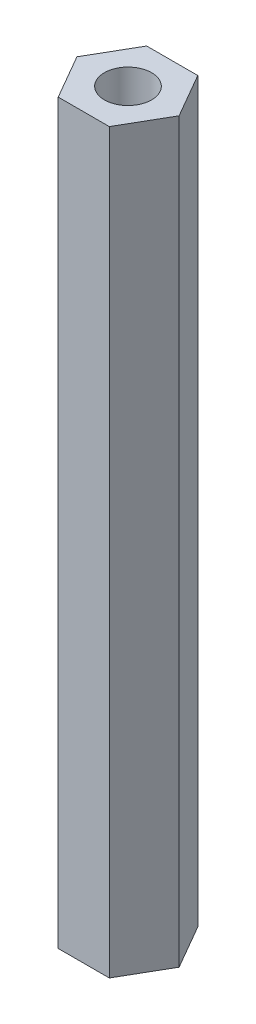
SolidWorks part; units mm, degrees
material "黄铜"
ref_plane "前视基准面" through (0, 0, 0) normal (0, 0, 1) x (1, 0, 0)
ref_plane "上视基准面" through (0, 0, 0) normal (0, 1, 0) x (1, 0, 0)
ref_plane "右视基准面" through (0, 0, 0) normal (1, 0, 0) x (0, 0, -1)
sketch "草图1" plane through (0, 0, 0) normal (0, 1, 0) x (1, 0, 0)
  line L1 (3.4641, 0) -> (1.7321, 3)
  line L2 (1.7321, 3) -> (-1.7321, 3)
  line L3 (-1.7321, 3) -> (-3.4641, 0)
  line L4 (-3.4641, 0) -> (-1.7321, -3)
  line L5 (-1.7321, -3) -> (1.7321, -3)
  line L6 (1.7321, -3) -> (3.4641, 0)
  circle A0 centre (0, 0) radius 3 construction
  dimension "D1" = 6
extrude "凸台-拉伸1" add sketch "草图1" along normal blind 50
sketch "草图2" plane through (0, 50, 0) normal (0, 1, 0) x (1, 0, 0)
  circle A0 centre (0, 0) radius 1.6
  dimension "D1" = 3.2
extrude "切除-拉伸1" cut sketch "草图2" against normal through all
